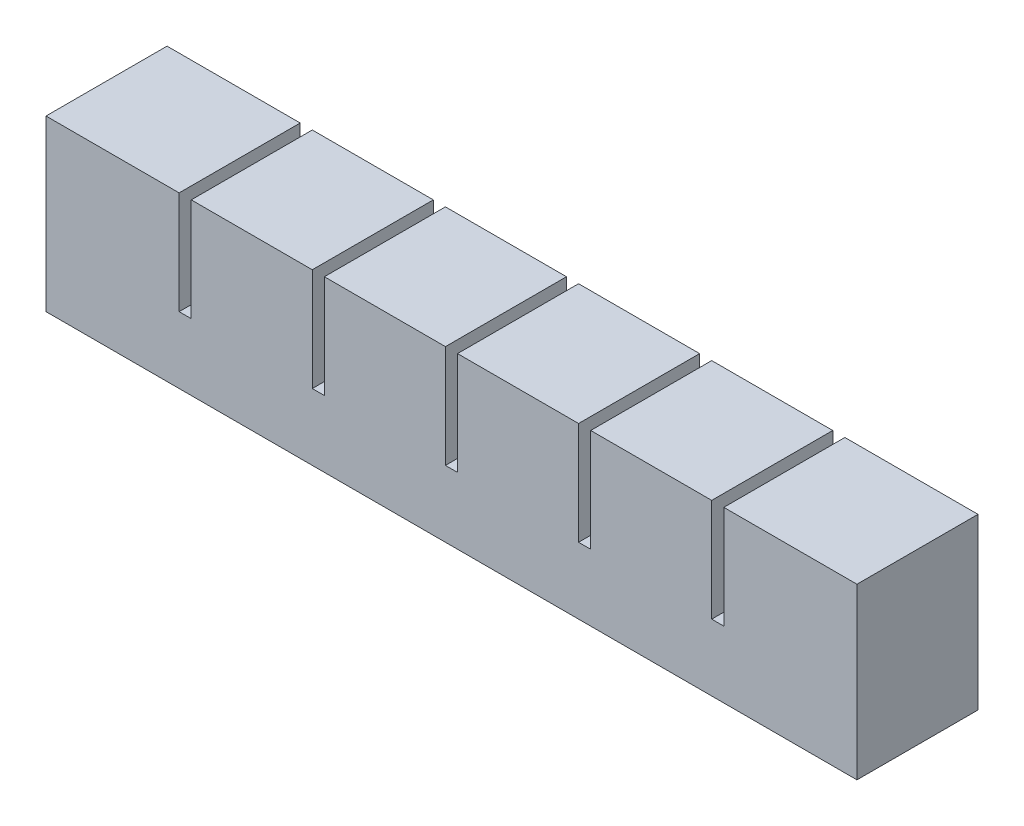
SolidWorks part; units mm, degrees
ref_plane "Front Plane" through (0, 0, 0) normal (0, 0, 1) x (1, 0, 0)
ref_plane "Top Plane" through (0, 0, 0) normal (0, 1, 0) x (1, 0, 0)
ref_plane "Right Plane" through (0, 0, 0) normal (1, 0, 0) x (0, 0, -1)
sketch "Sketch1" plane through (0, 0, 0) normal (0, 0, 1) x (1, 0, 0)
  line L1 (0, 0) -> (20, 0)
  line L2 (0, 0) -> (0, 22)
  line L3 (0, 22) -> (20, 22)
  line L4 (20, 0) -> (20, 22)
  dimension "D1" = 20
  dimension "D2" = 22
extrude "Boss-Extrude1" add sketch "Sketch1" along normal blind 20
sketch "Sketch2" plane through (0, 0, 0) normal (0, -1, 0) x (-1, 0, 0)
  line L0 (-20, -20) -> (-20, 0) construction
  line L1 (-6, -14) -> (-14, -14)
  line L2 (-6, -14) -> (-6, -6)
  line L3 (-6, -6) -> (-14, -6)
  line L4 (-14, -14) -> (-14, -6)
  line L5 (0, -20) -> (-20, -20) construction
  line L6 (0, -20) -> (0, 0) construction
  line L7 (0, 0) -> (-20, 0) construction
  dimension "D1" = 6
  dimension "D2" = 6
  dimension "D3" = 6
  dimension "D4" = 6
extrude "Cut-Extrude1" cut sketch "Sketch2" against normal blind 16
sketch "Sketch3" plane through (20, 0, 0) normal (1, 0, 0) x (0, 0, -1)
  line L0 (-20, 0) -> (-20, 22) construction
  line L1 (-20, 5) -> (0, 5)
  line L2 (-20, 5) -> (-20, 0)
  line L3 (-20, 0) -> (0, 0)
  line L4 (0, 5) -> (0, 0)
  dimension "D1" = 5
extrude "Boss-Extrude2" add sketch "Sketch3" along normal blind 2
pattern_linear "LPattern1" count 6 spacing 22 along (1, 0, 0) of bodies 103
combine bodies "Combine1" operation type add bodies to combine 104 105 106 107 108 103
sketch "Sketch4" plane through (130, 0, 0) normal (1, 0, 0) x (0, 0, -1)
  line L1 (-20, 22) -> (0, 22)
  line L2 (-20, 22) -> (-20, 5)
  line L3 (-20, 5) -> (0, 5)
  line L4 (0, 22) -> (0, 5)
extrude "Boss-Extrude3" add sketch "Sketch4" along normal up to surface (2 mm away) up to face at (132, 2.5, 10)
sketch "Sketch5" plane through (0, 0, 0) normal (-1, 0, 0) x (0, 0, 1)
  line L1 (0, 22) -> (20, 22)
  line L2 (0, 22) -> (0, 0)
  line L3 (0, 0) -> (20, 0)
  line L4 (20, 22) -> (20, 0)
extrude "Boss-Extrude4" add sketch "Sketch5" along normal blind 2
ref_point "Point1"
sketch "Sketch6" plane through (0, 0, 0) normal (0, -1, 0) x (1, 0, 0)
  line L0 (124, 6) -> (124, 14) construction
  line L1 (6, 9) -> (124, 9)
  line L2 (6, 9) -> (6, 11)
  line L3 (6, 11) -> (124, 11)
  line L4 (124, 9) -> (124, 11)
  line L5 (6, 9) -> (124, 11) construction
  line L6 (6, 11) -> (124, 9) construction
  point P0 (65, 10)
  dimension "D1" = 2
extrude "Cut-Extrude2" cut sketch "Sketch6" against normal blind 2
sketch "Sketch7" plane through (0, 0, 0) normal (0, -1, 0) x (-1, 0, 0)
  line L1 (2, -20) -> (-132, -20)
  line L2 (2, -20) -> (2, 0)
  line L3 (2, 0) -> (-132, 0)
  line L4 (-132, -20) -> (-132, 0)
extrude "Boss-Extrude5" add sketch "Sketch7" along normal blind 6
